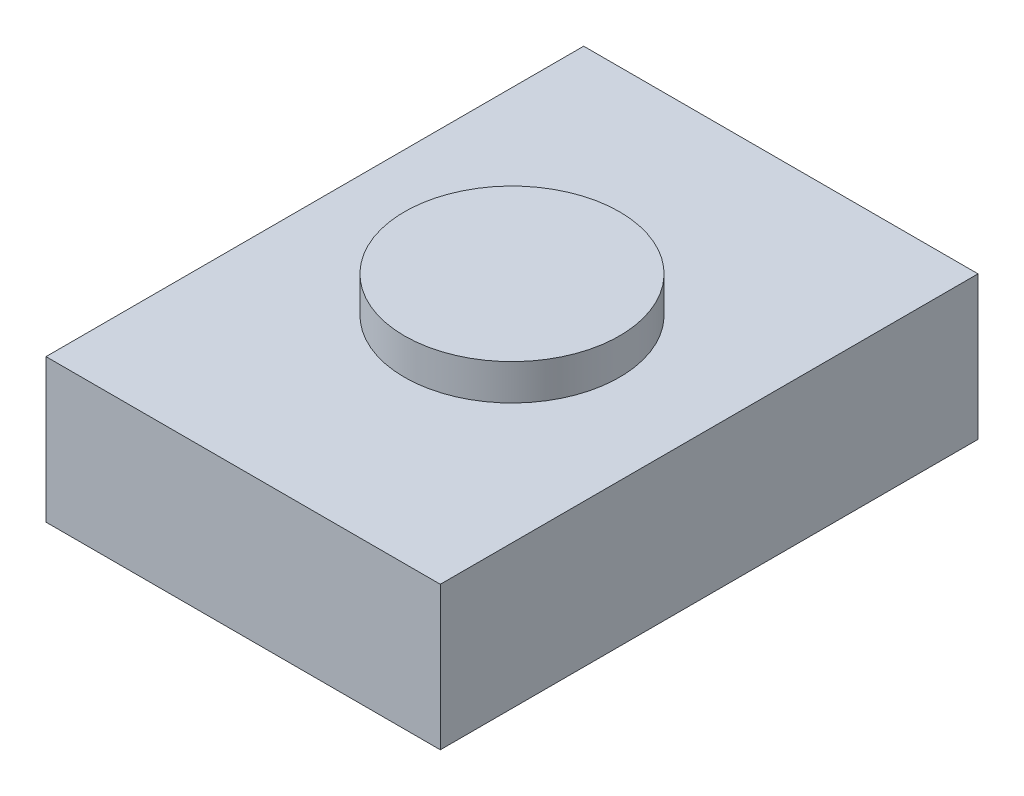
SolidWorks part; units mm, degrees
ref_plane "Front" through (0, 0, 0) normal (0, 0, 1) x (1, 0, 0)
ref_plane "Top" through (0, 0, 0) normal (0, 1, 0) x (1, 0, 0)
ref_plane "Right" through (0, 0, 0) normal (1, 0, 0) x (0, 0, -1)
sketch "Sketch1" plane through (0, 0, 0) normal (0, 1, 0) x (1, 0, 0)
  line L1 (-1.397, 1.905) -> (1.397, 1.905)
  line L2 (-1.397, 1.905) -> (-1.397, -1.905)
  line L3 (-1.397, -1.905) -> (1.397, -1.905)
  line L4 (1.397, 1.905) -> (1.397, -1.905)
  line L5 (-1.397, 1.905) -> (1.397, -1.905) construction
  line L6 (-1.397, -1.905) -> (1.397, 1.905) construction
  point P0 (0, 0)
  dimension "D1" = 3.81
  dimension "D2" = 2.794
extrude "Boss-Extrude1" add sketch "Sketch1" along normal blind 1.016
sketch "Sketch2" plane through (0, 1.016, 0) normal (0, 1, 0) x (1, 0, 0)
  circle A0 centre (0, 0) radius 0.762
  dimension "D1" = 1.524
extrude "Boss-Extrude2" add sketch "Sketch2" along normal blind 0.254
